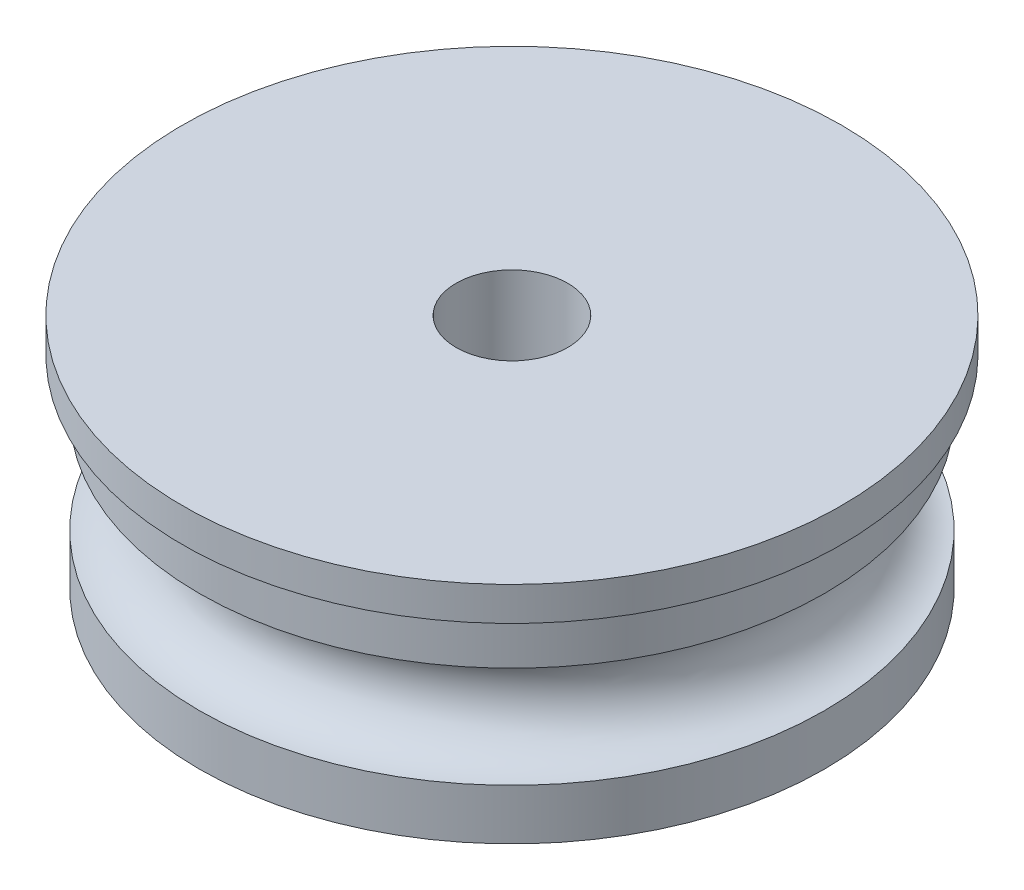
SolidWorks part; units mm, degrees
material "Alloy Steel"
ref_plane "Front Plane" through (0, 0, 0) normal (0, 0, 1) x (1, 0, 0)
ref_plane "Top Plane" through (0, 0, 0) normal (0, 1, 0) x (1, 0, 0)
ref_plane "Right Plane" through (0, 0, 0) normal (1, 0, 0) x (0, 0, -1)
sketch "Sketch1" plane through (0, 0, 0) normal (0, 0, 1) x (1, 0, 0)
  line L0 (0, 0) -> (-9.25, 0)
  line L1 (0, 0) -> (0, 7)
  line L2 (0, 7) -> (-9.75, 7)
  line L3 (-9.75, 7) -> (-9.75, 6)
  line L4 (-9.75, 6) -> (-9.25, 6)
  line L5 (-9.25, 6) -> (-9.25, 4.5)
  line L6 (-9.25, 0) -> (-9.25, 1.5)
  arc A1 (-9.25, 4.5) -> (-9.25, 1.5) centre (-9.25, 3) cw
  dimension "D1" = 9.25
  dimension "D5" = 1.5
  dimension "D2" = 7
  dimension "D3" = 9.75
  dimension "D4" = 1
  dimension "D6" = 3
revolve "Revolve1" add sketch "Sketch1" angle 360 about L1
sketch "Sketch4" plane through (0, 0, 0) normal (0, -1, 0) x (1, 0, 0)
  circle A0 centre (0, 0) radius 6
  dimension "D1" = 12
extrude "Cut-Extrude1" cut sketch "Sketch4" against normal blind 3
sketch "Sketch7" plane through (0, 7, 0) normal (0, 1, 0) x (1, 0, 0)
  point P0 (0, 0)
hole_wizard "M4x0.7 Tapped Hole1" positions "Sketch7" profile "Sketch8" tap size "M4x0.7" standard "ANSI Metric"
sketch "Sketch8" plane through (0, 7, 0) normal (1, 0, 0) x (0, 0, 1)
  line L0 (0, 0) -> (0, 4.9914)
  line L1 (0, 4.9914) -> (1.65, 4)
  line L2 (1.65, 4) -> (1.65, 0)
  line L5 (1.65, 0) -> (0, 0)
  line L10 (0, 4.9914) -> (-1.65, 4) construction
  line L11 (0, -6.35) -> (0, 107.95) construction
  dimension "Tap Drill Dia." = 3.3
  dimension "Tap Drill Depth" = 4
  dimension "Drill Angle" = 118
cosmetic thread "Hole Thread1" parameters "D1"=8, "D2"=4
